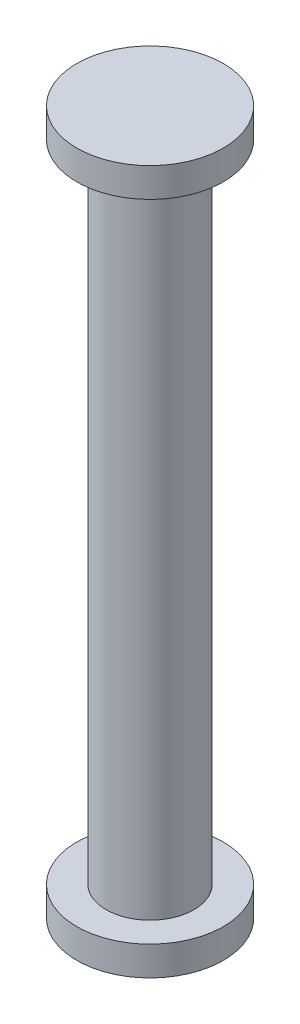
SolidWorks part; units mm, degrees
ref_plane "Front Plane" through (0, 0, 0) normal (0, 0, 1) x (1, 0, 0)
ref_plane "Top Plane" through (0, 0, 0) normal (0, 1, 0) x (1, 0, 0)
ref_plane "Right Plane" through (0, 0, 0) normal (1, 0, 0) x (0, 0, -1)
sketch "Sketch1" plane through (0, 0, 0) normal (0, 0, 1) x (1, 0, 0)
  line L0 (0, 0) -> (0, 24)
  line L1 (0, 24) -> (-2.5, 24)
  line L2 (-2.5, 24) -> (-2.5, 23)
  line L3 (-2.5, 23) -> (-1.5, 23)
  line L4 (-1.5, 23) -> (-1.5, 1)
  line L5 (-1.5, 1) -> (-2.5, 1)
  line L6 (-2.5, 1) -> (-2.5, 0)
  line L7 (-2.5, 0) -> (0, 0)
  dimension "D1" = 24
  dimension "D2" = 1
  dimension "D3" = 1
  dimension "D4" = 2.5
  dimension "D5" = 1.5
revolve "Revolve1" add sketch "Sketch1" angle 360 about L0
